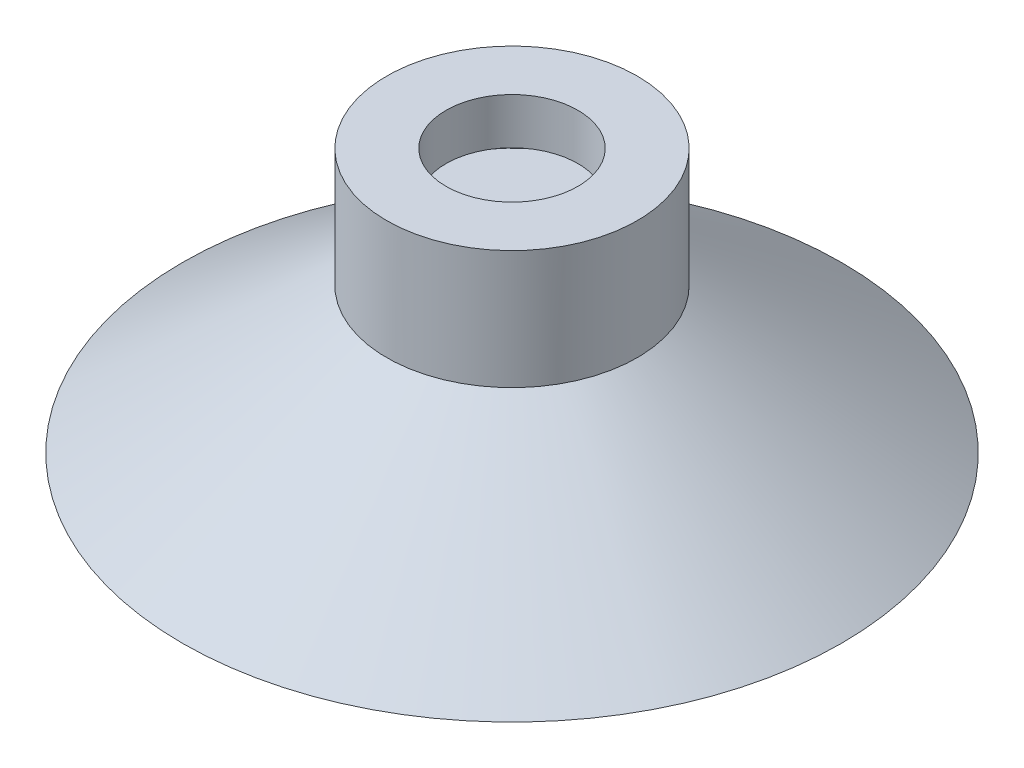
SolidWorks part; units mm, degrees
ref_plane "前视基准面" through (0, 0, 0) normal (0, 0, 1) x (1, 0, 0)
ref_plane "上视基准面" through (0, 0, 0) normal (0, 1, 0) x (1, 0, 0)
ref_plane "右视基准面" through (0, 0, 0) normal (1, 0, 0) x (0, 0, -1)
sketch "草图4" plane through (0, 0, 0) normal (0, 1, 0) x (1, 0, 0)
  circle A0 centre (0, 0) radius 9.5
  dimension "D1" = 19
extrude "凸台-拉伸1" add sketch "草图4" along normal blind 9
sketch "草图5" plane through (0, 9, 0) normal (0, 1, 0) x (1, 0, 0)
  circle A0 centre (0, 0) radius 5
  dimension "D1" = 10
extrude "切除-拉伸1" cut sketch "草图5" against normal blind 3.5
sketch "草图6" plane through (0, 5.5, 0) normal (0, 1, 0) x (1, 0, 0)
  circle A0 centre (0, 0) radius 8.5
  dimension "D1" = 17
extrude "切除-拉伸2" cut sketch "草图6" against normal blind 2.5
sketch "草图7" plane through (0, 0, 0) normal (0, 0, 1) x (1, 0, 0)
  line L0 (0, 0) -> (0, 15.3241)
  line L1 (-9.5, 0) -> (9.5, 0) construction
sketch "草图8" plane through (0, 0, 0) normal (0, 0, 1) x (1, 0, 0)
  line L0 (9.5, 0) -> (25, -11)
  line L3 (25, -11) -> (21.5443, -11)
  line L4 (21.5443, -11) -> (6.0443, 0)
  line L5 (-9.5, 0) -> (9.5, 0) construction
  line L6 (6.0443, 0) -> (9.5, 0)
  line L7 (0, 0) -> (0, 15.3241) construction
  dimension "D1" = 2
  dimension "D2" = 25
  dimension "D3" = 11
revolve "旋转3" add sketch "草图8" angle 360 about L0
